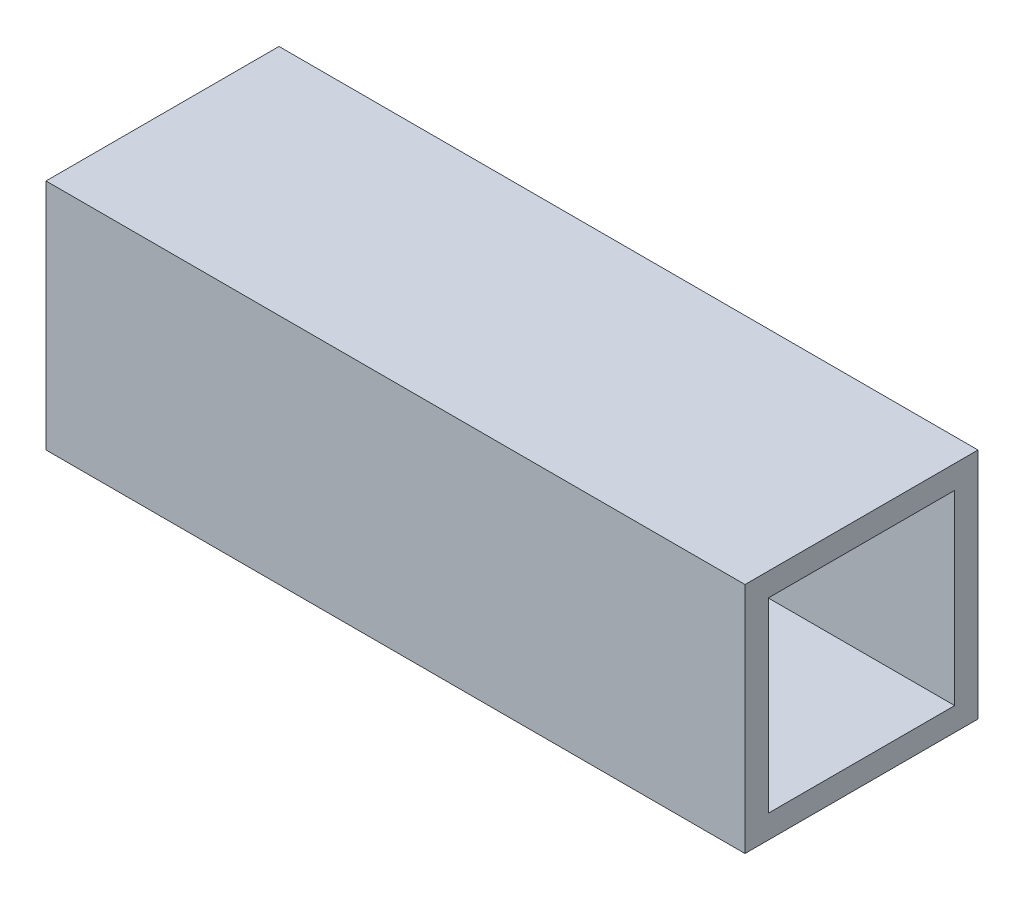
SolidWorks part; units mm, degrees
ref_plane "Front Plane" through (0, 0, 0) normal (0, 0, 1) x (1, 0, 0)
ref_plane "Top Plane" through (0, 0, 0) normal (0, 1, 0) x (1, 0, 0)
ref_plane "Right Plane" through (0, 0, 0) normal (1, 0, 0) x (0, 0, -1)
sketch "Sketch1" plane through (0, 0, 0) normal (1, 0, 0) x (0, 0, -1)
  line L0 (-6, 6) -> (6, 6)
  line L1 (-7.5, 7.5) -> (7.5, 7.5)
  line L2 (-7.5, 7.5) -> (-7.5, -7.5)
  line L3 (-7.5, -7.5) -> (7.5, -7.5)
  line L4 (7.5, 7.5) -> (7.5, -7.5)
  line L5 (-7.5, 7.5) -> (7.5, -7.5) construction
  line L6 (-7.5, -7.5) -> (7.5, 7.5) construction
  line L7 (6, 6) -> (6, -6)
  line L8 (-6, -6) -> (6, -6)
  line L9 (-6, 6) -> (-6, -6)
  point P0 (0, 0)
  dimension "D1" = 15
  dimension "D2" = 15
  dimension "D3" = 1.5
extrude "Boss-Extrude1" add sketch "Sketch1" along normal blind 45
sketch "Sketch2" plane through (0, 7.5, 0) normal (0, 1, 0) x (1, 0, 0)
  line L0 (0, 0) -> (45, 0) construction
  line L1 (45, 7.5) -> (45, -7.5) construction
  circle A0 centre (22.5, 0) radius 2
  dimension "D1" = 4
extrude "Cut-Extrude1" [suppressed] cut sketch "Sketch2" against normal through all
